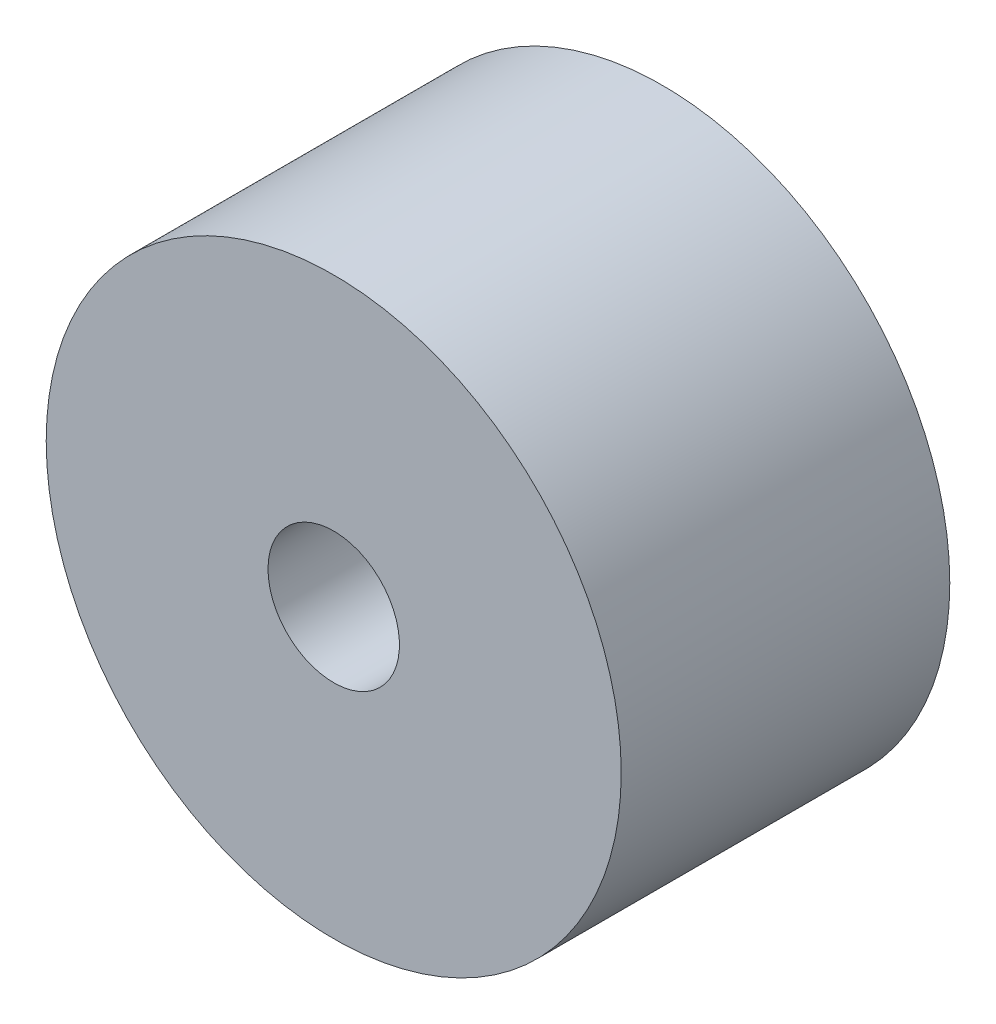
SolidWorks part; units mm, degrees
ref_plane "Front Plane" through (0, 0, 0) normal (0, 0, 1) x (1, 0, 0)
ref_plane "Top Plane" through (0, 0, 0) normal (0, 1, 0) x (1, 0, 0)
ref_plane "Right Plane" through (0, 0, 0) normal (1, 0, 0) x (0, 0, -1)
sketch "Sketch2" plane through (0, 0, 0) normal (0, 0, 1) x (1, 0, 0)
  circle A0 centre (0, 0) radius 17.5
  dimension "D1" = 35
extrude "Boss-Extrude1" add sketch "Sketch2" along normal blind 20
sketch "Sketch3" plane through (0, 0, 0) normal (0, 0, -1) x (-1, 0, 0)
  circle A0 centre (0, 0) radius 4
  dimension "D1" = 8
extrude "Cut-Extrude1" cut sketch "Sketch3" against normal through all
